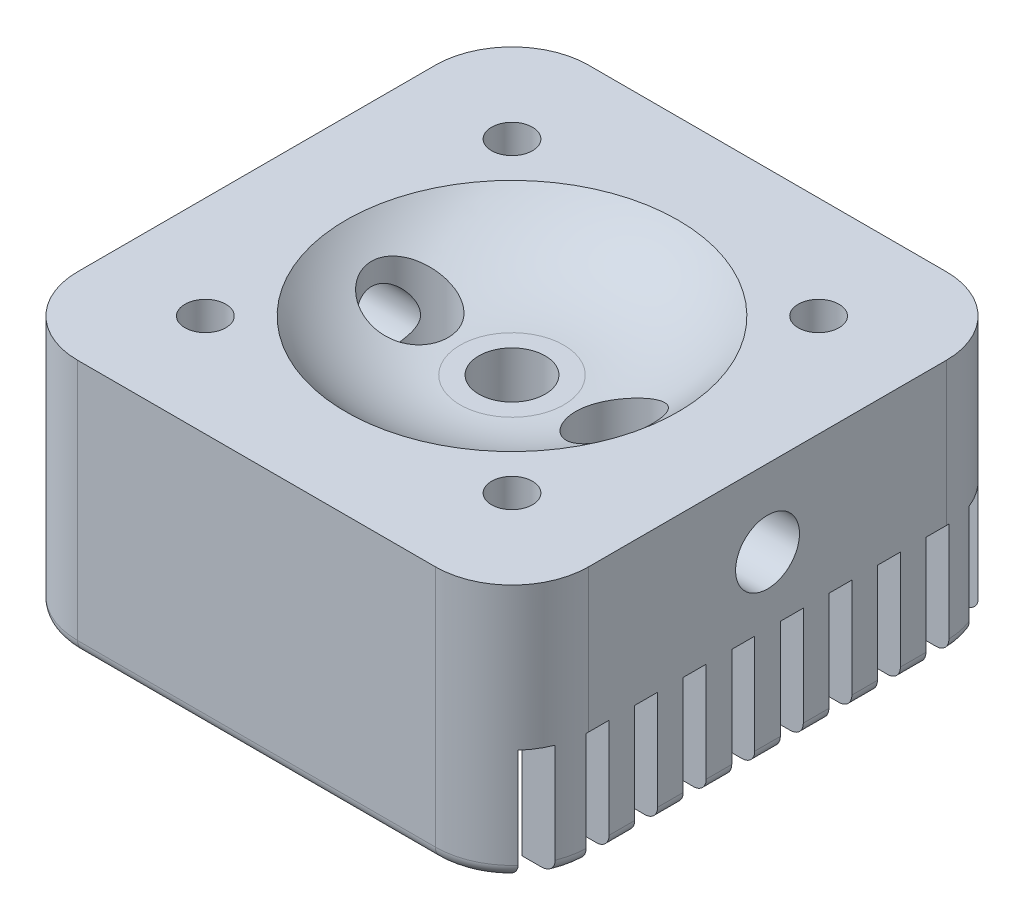
SolidWorks part; units mm, degrees
material "AISI 304"
ref_plane "Front Plane" through (0, 0, 0) normal (0, 0, 1) x (1, 0, 0)
ref_plane "Top Plane" through (0, 0, 0) normal (0, 1, 0) x (1, 0, 0)
ref_plane "Right Plane" through (0, 0, 0) normal (1, 0, 0) x (0, 0, -1)
sketch "Sketch1" plane through (0, 0, 0) normal (0, 1, 0) x (1, 0, 0)
  line L0 (-147.0046, 0) -> (147.0046, 0) construction
  line L1 (-70, 100) -> (70, 100)
  line L2 (-100, 70) -> (-100, -70)
  line L3 (-70, -100) -> (70, -100)
  line L4 (100, 70) -> (100, -70)
  line L5 (0, 129.7235) -> (0, -129.7235) construction
  arc A0 (-100, -70) -> (-70, -100) centre (-70, -70) ccw
  arc A1 (70, -100) -> (100, -70) centre (70, -70) ccw
  arc A2 (70, 100) -> (100, 70) centre (70, 70) cw
  arc A3 (-70, 100) -> (-100, 70) centre (-70, 70) ccw
  point P8 (0, 0)
  point P12 (0, 0)
  dimension "D2" = 30
  dimension "D1" = 200
extrude "Boss-Extrude1" add sketch "Sketch1" along normal blind 100
sketch "Sketch2" plane through (0, 0, 0) normal (1, 0, 0) x (0, 0, -1)
  line L0 (0, 0) -> (0, 111.6774) construction
  line L2 (0, 80) -> (20.2786, 80)
  line L3 (0, 100) -> (65, 100)
  line L4 (-70, 100) -> (70, 100) construction
  line L5 (0, 80) -> (0, 100)
  arc A0 (20.2786, 80) -> (65, 100) centre (20.2786, 140) ccw
  dimension "D2" = 60
  dimension "D1" = 20
  dimension "D3" = 130
revolve "Cut-Revolve1" cut sketch "Sketch2" angle 360 about L0
sketch "Sketch3" plane through (0, 80, 0) normal (0, 1, 0) x (1, 0, 0)
  circle A0 centre (0, 0) radius 13
  dimension "D1" = 26
extrude "Cut-Extrude1" cut sketch "Sketch3" against normal up to next
sketch "Sketch6" plane through (0, 100, 0) normal (0, 1, 0) x (1, 0, 0)
  line L0 (0, 74.3014) -> (0, -74.3014) construction
  circle A0 centre (40, 0) radius 15
  circle A1 centre (-40, 0) radius 15
  point P8 (0, 0)
  dimension "D1" = 30
  dimension "D2" = 40
extrude "Cut-Extrude4" cut sketch "Sketch6" against normal through all
sketch "Sketch7" plane through (-100, 0, 0) normal (-1, 0, 0) x (0, 0, 1)
  circle A0 centre (0, 70) radius 12.5
  dimension "D1" = 25
  dimension "D2" = 70
extrude "Cut-Extrude5" cut sketch "Sketch7" against normal up to next
sketch "Sketch12" plane through (0, 100, 0) normal (0, 1, 0) x (1, 0, 0)
  line L0 (0, 115.7368) -> (0, -115.7368) construction
  line L1 (-124.4026, 0) -> (124.4026, 0) construction
  circle A0 centre (-60, 60) radius 8
  circle A2 centre (60, 60) radius 8
  circle A3 centre (60, -60) radius 8
  circle A4 centre (-60, -60) radius 8
  point P8 (0, 0)
  point P14 (0, 0)
  dimension "D1" = 16
  dimension "D2" = 60
  dimension "D3" = 60
extrude "Cut-Extrude9" cut sketch "Sketch12" against normal up to next
mirror "Mirror2" about plane through (0, 0, 0) normal (1, 0, 0) of "Cut-Extrude5"
sketch "Sketch9" plane through (0, 0, 0) normal (0, -1, 0) x (1, 0, 0)
  line L0 (-100, -70) -> (-100, 70) construction
  line L1 (-85, 85) -> (85, 85)
  line L2 (-85, 85) -> (-85, -85)
  line L3 (-85, -85) -> (85, -85)
  line L4 (85, 85) -> (85, -85)
  line L5 (-70, 100) -> (70, 100) construction
  line L6 (70, -100) -> (-70, -100) construction
  dimension "D1" = 15
  dimension "D2" = 15
  dimension "D3" = 15
extrude "Cut-Extrude6" cut sketch "Sketch9" against normal blind 44
fillet "Fillet1" radius 5 8 edges at (91.2132, 0, 91.2132) (0, 0, 100) (-91.2132, 0, 91.2132) (-100, 0, 0) (-91.2132, 0, -91.2132) (0, 0, -100) (91.2132, 0, -91.2132) (100, 0, 0)
ref_plane "Plane1" through (0, 0, 0) normal (0, -1, 0) x (-1, 0, 0)
sketch "Sketch10" plane through (-100, 0, 0) normal (-1, 0, 0) x (0, 0, 1)
  line L42 (-90, 44) -> (-81, 44)
  line L43 (-90, 44) -> (-90, 0)
  line L44 (-90, 0) -> (-81, 0)
  line L45 (-81, 44) -> (-81, 0)
  line L46 (-95, 0) -> (-70, 0) construction
  dimension "D4" = 9
  dimension "D5" = 10
extrude "Cut-Extrude7" cut sketch "Sketch10" against normal through all
pattern_linear "LPattern1" count 10 spacing 19 along (0, 0, 1) of "Cut-Extrude7"
